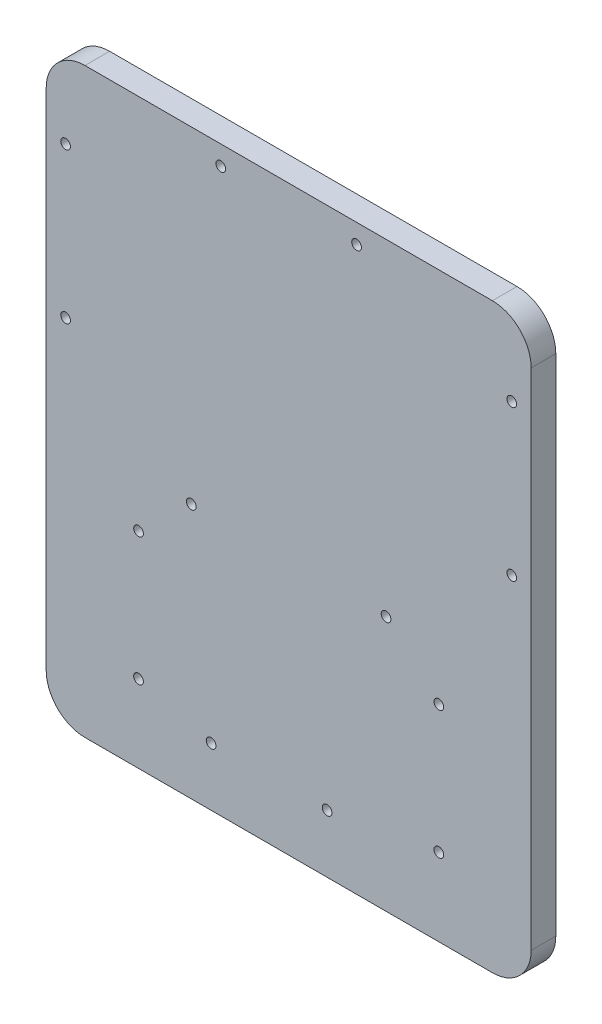
SolidWorks part; units mm, degrees
ref_plane "Front Plane" through (0, 0, 0) normal (0, 0, 1) x (1, 0, 0)
ref_plane "Top Plane" through (0, 0, 0) normal (0, 1, 0) x (1, 0, 0)
ref_plane "Right Plane" through (0, 0, 0) normal (1, 0, 0) x (0, 0, -1)
sketch "Sketch1" plane through (0, 0, 0) normal (0, 0, 1) x (1, 0, 0)
  line L0 (0, -75) -> (0, 75) construction
  line L1 (-62.5, 75) -> (62.5, 75)
  line L2 (-62.5, 75) -> (-62.5, -75)
  line L3 (-62.5, -75) -> (62.5, -75)
  line L4 (62.5, 75) -> (62.5, -75)
  line L5 (-62.5, 75) -> (62.5, -75) construction
  line L6 (-62.5, -75) -> (62.5, 75) construction
  line L7 (-25.1, -9.2) -> (25.1, -9.2) construction
  line L8 (-25.1, -9.2) -> (-25.1, -60) construction
  line L9 (-25.1, -60) -> (25.1, -60) construction
  line L10 (25.1, -9.2) -> (25.1, -60) construction
  line L11 (-17.5, 75) -> (-17.5, 70) construction
  line L12 (-17.5, 70) -> (17.5, 70) construction
  line L13 (17.5, 70) -> (17.5, 75) construction
  line L14 (38.7, -75) -> (38.7, 75) construction
  line L15 (-38.7, -75) -> (-38.7, 75) construction
  circle A0 centre (-25.1, -9.2) radius 1.25
  circle A1 centre (25.1, -9.2) radius 1.25
  circle A2 centre (-20, -60) radius 1.25
  circle A3 centre (9.9, -60) radius 1.25
  circle A4 centre (-17.5, 70) radius 1.25
  circle A5 centre (17.5, 70) radius 1.25
  circle A6 centre (38.7, -55) radius 1.25
  circle A7 centre (38.7, -22) radius 1.25
  circle A8 centre (-38.7, -22) radius 1.25
  circle A9 centre (-38.7, -55) radius 1.25
  point P0 (0, 0)
  point P6 (0, -60)
  point P21 (0, 70)
  dimension "D4" = 2.5
  dimension "D7" = 29.9
  dimension "D8" = 15.2
  dimension "D13" = 33
  dimension "D1" = 150
  dimension "D2" = 125
  dimension "D3" = 15
  dimension "D5" = 50.8
  dimension "D6" = 5.1
  dimension "D9" = 35
  dimension "D10" = 5
  dimension "D11" = 23.8
  dimension "D12" = 20
extrude "Boss-Extrude1" add sketch "Sketch1" along normal blind 6.35
fillet "Fillet1" radius 10 4 edges at (-62.5, -75, 3.175) (62.5, -75, 3.175) (62.5, 75, 3.175) (-62.5, 75, 3.175)
sketch "Sketch2" plane through (0, 0, 6.35) normal (0, 0, 1) x (1, 0, 0)
  line L0 (57.5, -75) -> (57.5, 75) construction
  line L1 (-52.5, -75) -> (52.5, -75) construction
  line L2 (52.5, 75) -> (-52.5, 75) construction
  line L3 (62.5, -65) -> (62.5, 65) construction
  line L4 (0, -75) -> (0, 75) construction
  line L5 (-57.5, -75) -> (-57.5, 75) construction
  circle A0 centre (57.5, 55) radius 1.25
  circle A1 centre (57.5, 16.2) radius 1.25
  circle A2 centre (-57.5, 16.2) radius 1.25
  circle A3 centre (-57.5, 55) radius 1.25
  dimension "D2" = 2.5
  dimension "D3" = 38.8
  dimension "D4" = 20
  dimension "D1" = 5
extrude "Cut-Extrude1" cut sketch "Sketch2" against normal up to next
